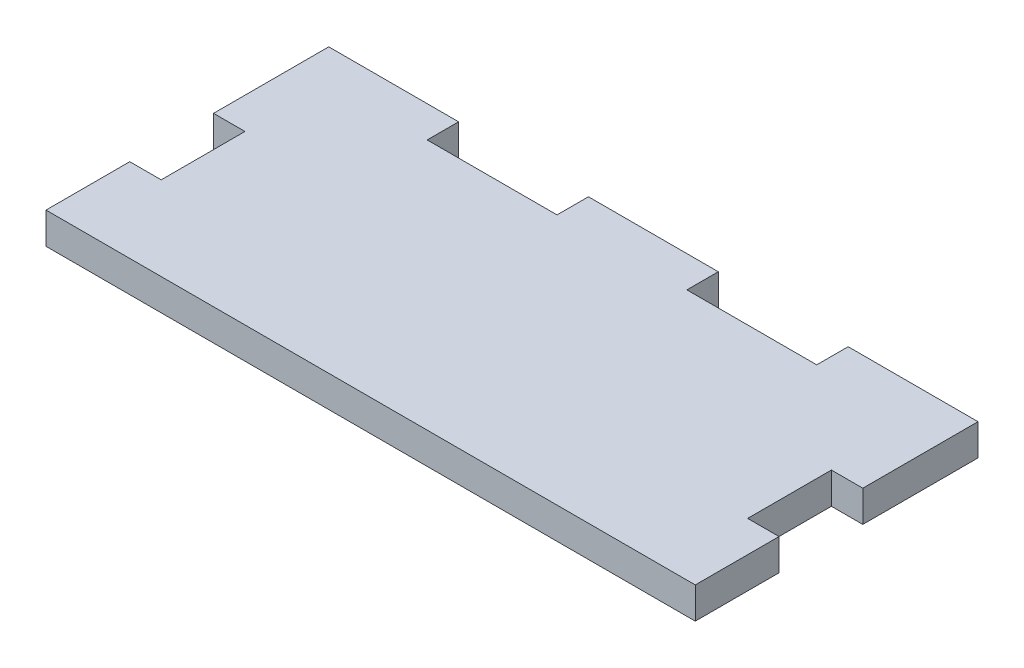
SolidWorks part; units mm, degrees
ref_plane "Ön Düzlem" through (0, 0, 0) normal (0, 0, 1) x (1, 0, 0)
ref_plane "Üst Düzlem" through (0, 0, 0) normal (0, 1, 0) x (1, 0, 0)
ref_plane "Sağ Düzlem" through (0, 0, 0) normal (1, 0, 0) x (0, 0, -1)
sketch "Sketch1" plane through (0, 0, 0) normal (0, 1, 0) x (1, 0, 0)
  line L0 (-31, 13.5) -> (-18.6, 13.5)
  line L1 (31, -13.5) -> (-31, -13.5)
  line L2 (31, -13.5) -> (31, -5.5)
  line L3 (31, 13.5) -> (18.6, 13.5)
  line L4 (-31, -13.5) -> (-31, -5.5)
  line L7 (6.2, 13.5) -> (-6.2, 13.5)
  line L8 (-6.2, 13.5) -> (6.2, 13.5)
  line L9 (-31, -13.5) -> (-31, -5.5)
  line L10 (-18.6, 13.5) -> (-18.6, 10.5)
  line L11 (-18.6, 10.5) -> (-6.2, 10.5)
  line L12 (-31, -5.5) -> (-28, -5.5)
  line L13 (6.2, 10.5) -> (18.6, 10.5)
  line L14 (-28, -5.5) -> (-28, 2.5)
  line L15 (-28, 2.5) -> (-31, 2.5)
  line L16 (-6.2, 10.5) -> (-6.2, 13.5)
  line L17 (6.2, 10.5) -> (6.2, 13.5)
  line L18 (18.6, 13.5) -> (18.6, 10.5)
  line L19 (-18.6, 13.5) -> (-31, 13.5)
  line L20 (-31, 2.5) -> (-31, 13.5)
  line L22 (28, 2.5) -> (31, 2.5)
  line L23 (28, -5.5) -> (28, 2.5)
  line L24 (31, -5.5) -> (28, -5.5)
  line L25 (31, 2.5) -> (31, 13.5)
  point P0 (0, 0)
  dimension "D1" = 27
  dimension "D2" = 62
extrude "Boss-Extrude1" add sketch "Sketch1" along normal blind 3 contours L22 L25 L3 L18 L13 L17 L7 L16 L11 L10 L0 L20 L15 L14 L12 L4 L1 L2 L24 L23
